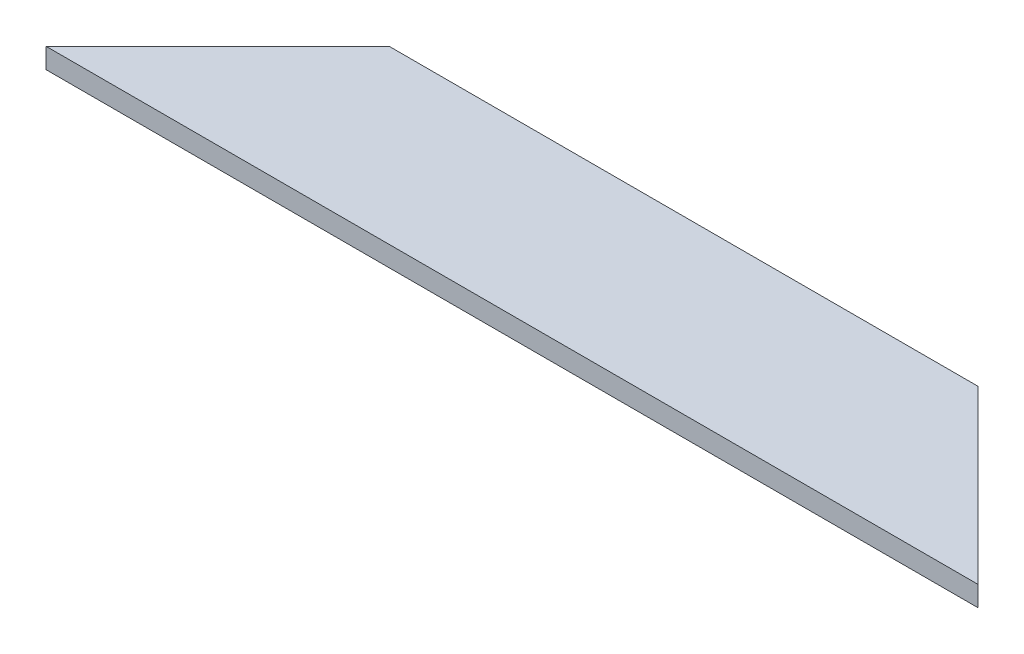
SolidWorks part; units mm, degrees
ref_plane "Front Plane" through (0, 0, 0) normal (0, 0, 1) x (1, 0, 0)
ref_plane "Top Plane" through (0, 0, 0) normal (0, 1, 0) x (1, 0, 0)
ref_plane "Right Plane" through (0, 0, 0) normal (1, 0, 0) x (0, 0, -1)
sketch "Sketch1" plane through (0, 0, 0) normal (0, 1, 0) x (1, 0, 0)
  line L0 (-92.5032, -30.4389) -> (-67.1032, -5.0389)
  line L1 (-67.1032, -5.0389) -> (20.0968, -5.0389)
  line L3 (-92.5032, -30.4389) -> (45.4968, -30.4389)
  line L5 (45.4968, -30.4389) -> (20.0968, -5.0389)
extrude "Boss-Extrude1" add sketch "Sketch1" along normal blind 3
